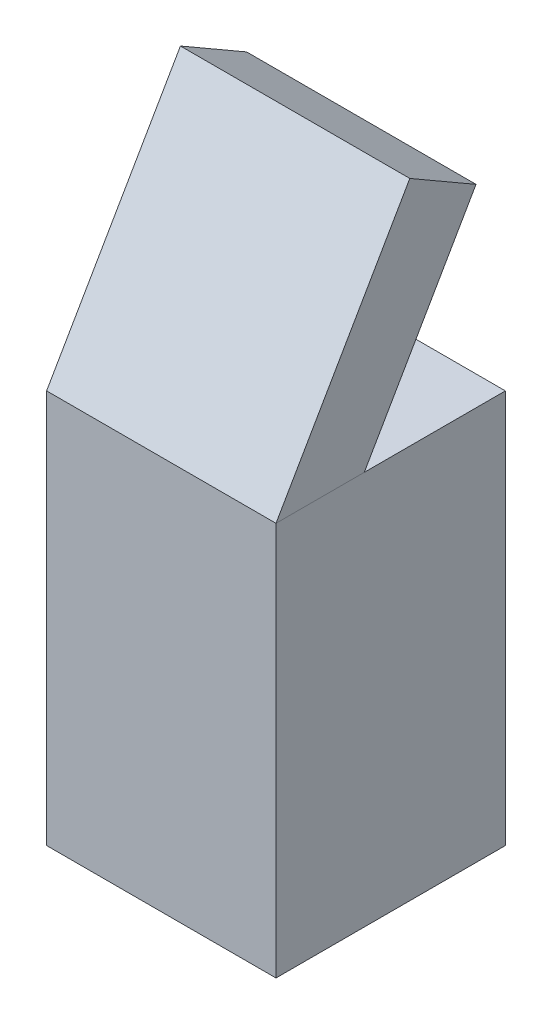
SolidWorks part; units mm, degrees
ref_plane "前视基准面" through (0, 0, 0) normal (0, 0, 1) x (1, 0, 0)
ref_plane "上视基准面" through (0, 0, 0) normal (0, 1, 0) x (1, 0, 0)
ref_plane "右视基准面" through (0, 0, 0) normal (1, 0, 0) x (0, 0, -1)
sketch "草图1" plane through (0, 0, 0) normal (0, 1, 0) x (1, 0, 0)
  line L1 (-300, 300) -> (300, 300)
  line L2 (-300, 300) -> (-300, -300)
  line L3 (-300, -300) -> (300, -300)
  line L4 (300, 300) -> (300, -300)
  line L5 (-300, 300) -> (300, -300) construction
  line L6 (-300, -300) -> (300, 300) construction
  point P0 (0, 0)
extrude "拉伸1" add sketch "草图1" along normal blind 1030
sketch "草图4" plane through (300, 0, 0) normal (1, 0, 0) x (0, 0, -1)
  line L0 (-300, 1030) -> (50, 1636.2178)
  line L1 (50, 1636.2178) -> (223.2051, 1536.2178)
  line L2 (223.2051, 1536.2178) -> (-69.0599, 1030)
  line L3 (-300, 1030) -> (300, 1030) construction
  line L4 (-69.0599, 1030) -> (-300, 1030)
extrude "拉伸2" add sketch "草图4" against normal blind 600 separate body
